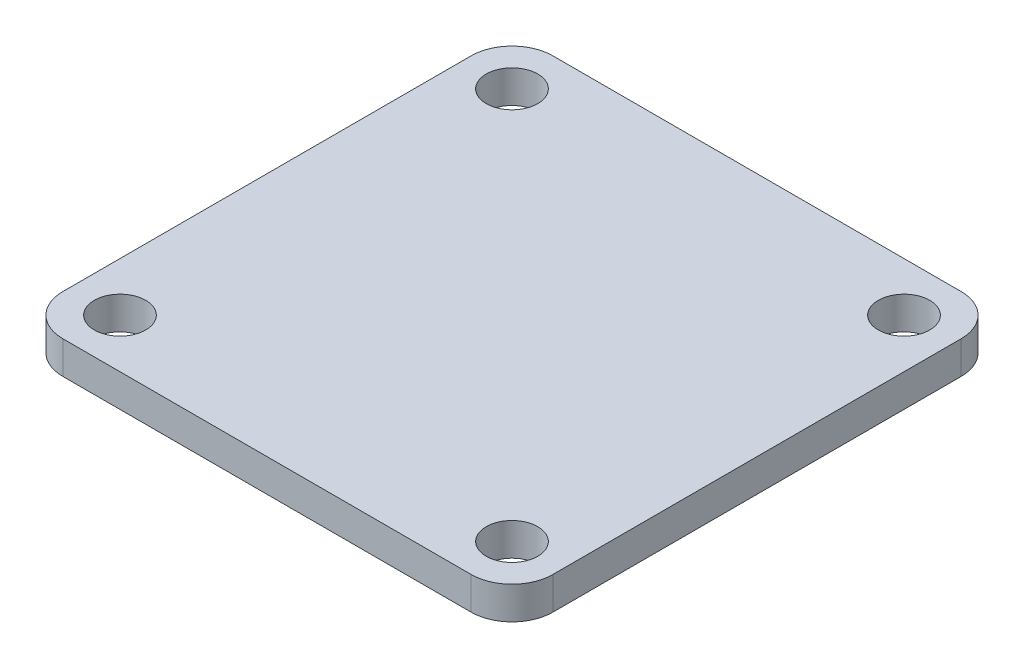
SolidWorks part; units mm, degrees
ref_plane "Front Plane" through (0, 0, 0) normal (0, 0, 1) x (1, 0, 0)
ref_plane "Top Plane" through (0, 0, 0) normal (0, 1, 0) x (1, 0, 0)
ref_plane "Right Plane" through (0, 0, 0) normal (1, 0, 0) x (0, 0, -1)
sketch "Sketch1" plane through (0, 0, 0) normal (0, 1, 0) x (1, 0, 0)
  line L1 (24, -24) -> (-24, -24) construction
  line L2 (24, -24) -> (24, 24) construction
  line L3 (24, 24) -> (-24, 24) construction
  line L4 (-24, -24) -> (-24, 24) construction
  line L5 (24, -24) -> (-24, 24) construction
  line L6 (24, 24) -> (-24, -24) construction
  line L7 (-30, -30) -> (30, -30)
  line L8 (-30, -30) -> (-30, 30)
  line L9 (-30, 30) -> (30, 30)
  line L10 (30, -30) -> (30, 30)
  line L11 (-30, -30) -> (30, 30) construction
  line L12 (-30, 30) -> (30, -30) construction
  circle A0 centre (-24, 24) radius 3.15
  circle A1 centre (24, 24) radius 3.15
  circle A2 centre (-24, -24) radius 3.15
  circle A3 centre (24, -24) radius 3.15
  point P0 (0, 0)
  point P10 (0, 0)
  dimension "D2" = 6.3
  dimension "D1" = 48
  dimension "D3" = 60
extrude "Boss-Extrude1" add sketch "Sketch1" along normal blind 4
fillet "Fillet1" radius 5 4 edges at (-30, 2, 30) (30, 2, 30) (30, 2, -30) (-30, 2, -30)
